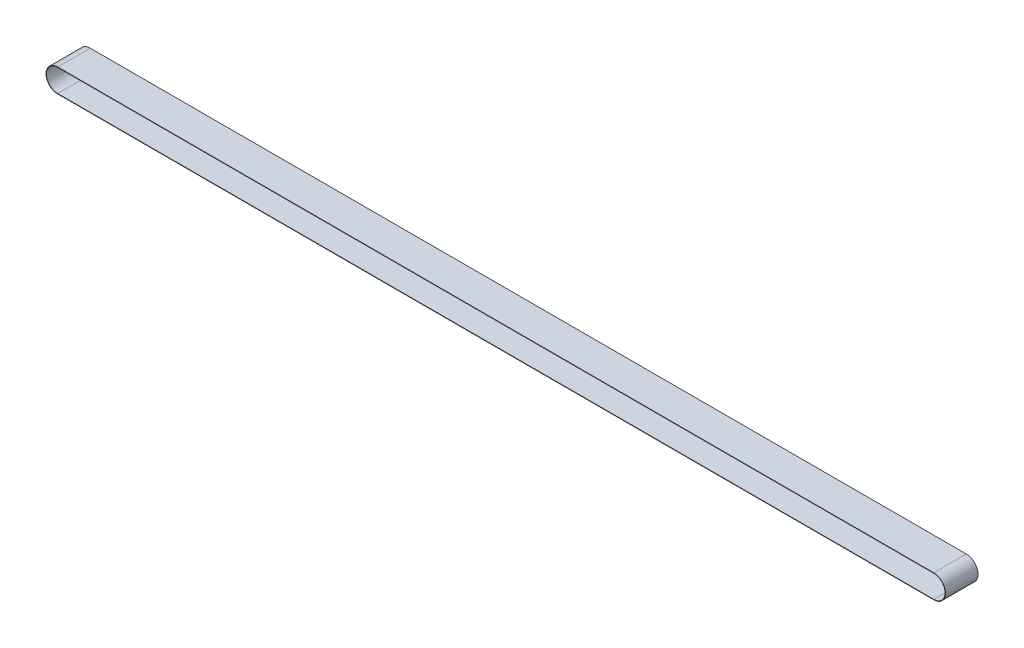
SolidWorks part; units mm, degrees
material "45#"
ref_plane "前视基准面" through (0, 0, 0) normal (0, 0, 1) x (1, 0, 0)
ref_plane "上视基准面" through (0, 0, 0) normal (0, 1, 0) x (1, 0, 0)
ref_plane "右视基准面" through (0, 0, 0) normal (1, 0, 0) x (0, 0, -1)
sketch "草图1" plane through (0, 0, 0) normal (0, 0, 1) x (1, 0, 0)
  line L0 (-1010, 0) -> (1010, 0) construction
  line L1 (-1010, 26) -> (1010, 26)
  line L2 (-1010, -26) -> (1010, -26)
  arc A0 (-1010, 26) -> (-1010, -26) centre (-1010, 0) ccw
  arc A1 (1010, -26) -> (1010, 26) centre (1010, 0) ccw
  point P3 (0, 0)
  dimension "D2" = 26
  dimension "D1" = 2020
extrude "拉伸-薄壁1" add sketch "草图1" along normal mid plane 75 thin thin type one direction wall 1
